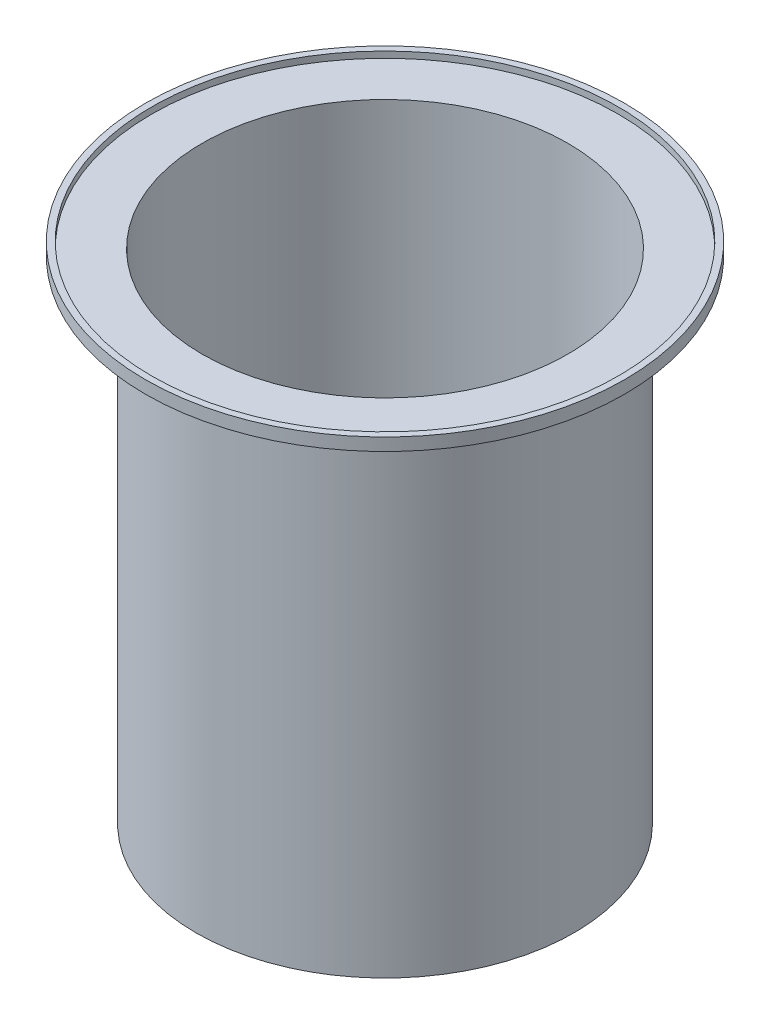
SolidWorks part; units mm, degrees
ref_plane "Front Plane" through (0, 0, 0) normal (0, 0, 1) x (1, 0, 0)
ref_plane "Top Plane" through (0, 0, 0) normal (0, 1, 0) x (1, 0, 0)
ref_plane "Right Plane" through (0, 0, 0) normal (1, 0, 0) x (0, 0, -1)
sketch "Sketch1" plane through (0, 0, 0) normal (1, 0, 0) x (0, 0, -1)
  line L0 (0, 329.9711) -> (0, -70.0289)
  line L1 (0, -70.0289) -> (-150, -70.0289)
  line L2 (-150, -70.0289) -> (-150, 319.9711)
  line L3 (-150, 319.9711) -> (-190, 319.9711)
  line L4 (-190, 319.9711) -> (-190, 329.9711)
  line L5 (-190, 329.9711) -> (0, 329.9711)
  dimension "D1" = 400
  dimension "D2" = 10
  dimension "D3" = 150
  dimension "D4" = 190
sketch "Sketch2" plane through (0, 0, 0) normal (1, 0, 0) x (0, 0, -1)
  line L0 (0, 438.3699) -> (0, -149.0153) construction
revolve "Revolve1" add sketch "Sketch1" angle 360 about L0
shell "Shell1" thickness 5
equation "\"D1@Sketch1\"=\"height@barrel.sldprt\" - 100"
equation "\"D3@Sketch1\"=\"barrelradius@barrel.sldprt\" - 50"
equation "\"D4@Sketch1\"=\"barrelradius@barrel.sldprt\" -10"
